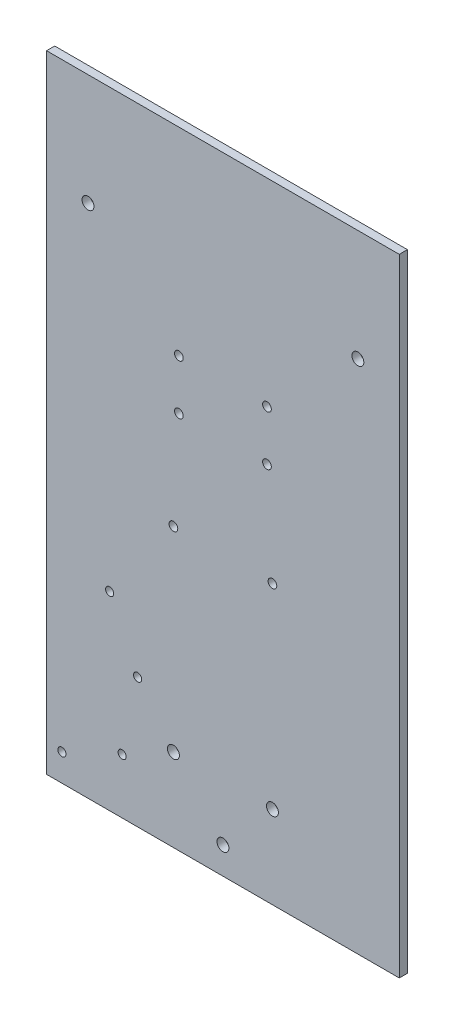
SolidWorks part; units mm, degrees
ref_plane "正面" through (0, 0, 0) normal (0, 0, 1) x (1, 0, 0)
ref_plane "平面" through (0, 0, 0) normal (0, 1, 0) x (1, 0, 0)
ref_plane "右側面" through (0, 0, 0) normal (1, 0, 0) x (0, 0, -1)
sketch "ｽｹｯﾁ1" plane through (0, 0, 0) normal (0, 0, 1) x (1, 0, 0)
  line L1 (-75, 115.5) -> (75, 115.5)
  line L2 (-75, 115.5) -> (-75, -115.5)
  line L3 (-75, -115.5) -> (75, -115.5)
  line L4 (75, 115.5) -> (75, -115.5)
  line L5 (-75, 115.5) -> (75, -115.5) construction
  line L6 (-75, -115.5) -> (75, 115.5) construction
  point P0 (0, 0)
  dimension "D1" = 231
  dimension "D2" = 150
extrude "ﾎﾞｽ - 押し出し1" add sketch "ｽｹｯﾁ1" along normal blind 12.5
sketch "ｽｹｯﾁ2" plane through (0, 0, 12.5) normal (0, 0, 1) x (1, 0, 0)
  line L0 (0, 115.5) -> (21.5, 115.5)
  line L1 (75, 115.5) -> (-75, 115.5) construction
  line L2 (0, 115.5) -> (-21.5, 115.5)
  line L3 (-21.5, 115.5) -> (-21.5, 13.5)
  line L4 (21.5, 115.5) -> (21.5, 13.5)
  line L5 (21.5, 13.5) -> (-21.5, 13.5)
  dimension "D1" = 21.5
  dimension "D2" = 21.5
  dimension "D3" = 102
extrude "ｶｯﾄ - 押し出し1" cut sketch "ｽｹｯﾁ2" against normal blind 10.5
sketch "ｽｹｯﾁ3" plane through (0, 0, 2) normal (0, 0, 1) x (1, 0, 0)
  line L0 (0, 115.5) -> (16.23, 115.5)
  line L1 (21.5, 115.5) -> (-21.5, 115.5) construction
  line L2 (0, 115.5) -> (-16.23, 115.5)
  line L3 (-16.23, 115.5) -> (-16.23, 42.5)
  line L4 (16.23, 115.5) -> (16.23, 42.5)
  line L5 (-16.23, 42.5) -> (-16.23, 24.1)
  line L6 (16.23, 42.5) -> (16.23, 24.1)
  line L7 (0, 115.5) -> (0, 110)
  circle A0 centre (-16.23, 42.5) radius 1.6
  circle A1 centre (16.23, 42.5) radius 1.6
  circle A2 centre (-16.23, 24.1) radius 1.6
  circle A3 centre (16.23, 24.1) radius 1.6
  circle A4 centre (0, 110) radius 4.4
  dimension "D5" = 3.2
  dimension "D6" = 3.2
  dimension "D9" = 3.2
  dimension "D10" = 3.2
  dimension "D12" = 8.8
  dimension "D1" = 16.23
  dimension "D2" = 16.23
  dimension "D3" = 73
  dimension "D4" = 73
  dimension "D7" = 18.4
  dimension "D8" = 18.4
  dimension "D11" = 5.5
sketch "ｽｹｯﾁ4" plane through (0, 0, 12.5) normal (0, 0, 1) x (1, 0, 0)
  line L0 (0, 115.5) -> (49.73, 115.5)
  line L1 (21.5, 115.5) -> (-21.5, 115.5) construction
  line L2 (75, 115.5) -> (21.5, 115.5) construction
  line L3 (0, 115.5) -> (-49.73, 115.5)
  line L4 (-21.5, 115.5) -> (-75, 115.5) construction
  line L5 (-49.73, 115.5) -> (-49.73, 74.5)
  line L6 (49.73, 115.5) -> (49.73, 74.5)
  circle A0 centre (-49.73, 74.5) radius 2.2
  circle A1 centre (49.73, 74.5) radius 2.2
  dimension "D5" = 4.4
  dimension "D6" = 4.4
  dimension "D1" = 49.73
  dimension "D2" = 49.73
  dimension "D3" = 41
  dimension "D4" = 41
extrude "ｶｯﾄ - 押し出し3" cut sketch "ｽｹｯﾁ4" against normal through all both and the other way through all
sketch "ｽｹｯﾁ5" plane through (0, 0, 12.5) normal (0, 0, 1) x (1, 0, 0)
  line L0 (0, 115.5) -> (18.25, 115.5)
  line L1 (21.5, 115.5) -> (-21.5, 115.5) construction
  line L2 (75, 115.5) -> (21.5, 115.5) construction
  line L3 (0, 115.5) -> (-18.25, 115.5)
  line L4 (-21.5, 115.5) -> (-75, 115.5) construction
  line L5 (-18.25, 115.5) -> (-18.25, -12.95)
  line L6 (18.25, 115.5) -> (18.25, -12.95)
  line L7 (-18.25, -12.95) -> (-18.25, -85)
  line L8 (18.25, -12.95) -> (18.25, -85)
  line L9 (0, -115.5) -> (0, -105.5)
  line L10 (-75, -115.5) -> (75, -115.5) construction
  line L11 (-18.25, -85) -> (-31.45, -85)
  line L12 (-31.45, -85) -> (-31.45, -67.68)
  line L13 (-31.45, -67.68) -> (-41.75, -67.68)
  line L14 (-41.75, -67.68) -> (-41.75, -45.48)
  line L15 (0, -105.5) -> (-37.14, -105.5)
  line L16 (-37.14, -105.5) -> (-37.14, -95.2)
  line L17 (-37.14, -105.5) -> (-59.34, -105.5)
  circle A0 centre (-18.25, -12.95) radius 1.6
  circle A1 centre (18.25, -12.95) radius 1.6
  circle A2 centre (-18.25, -85) radius 2.2
  circle A3 centre (18.25, -85) radius 2.2
  circle A4 centre (0, -105.5) radius 2.2
  circle A5 centre (-31.45, -67.68) radius 1.5
  circle A6 centre (-41.75, -45.48) radius 1.5
  circle A7 centre (-37.14, -95.2) radius 1.5
  circle A9 centre (-59.34, -105.5) radius 1.5
  dimension "D5" = 3.2
  dimension "D6" = 3.2
  dimension "D9" = 4.4
  dimension "D10" = 4.4
  dimension "D12" = 4.4
  dimension "D17" = 3
  dimension "D18" = 3
  dimension "D24" = 3
  dimension "D22" = 3
  dimension "D1" = 18.25
  dimension "D2" = 18.25
  dimension "D3" = 128.45
  dimension "D4" = 128.45
  dimension "D7" = 72.05
  dimension "D8" = 72.05
  dimension "D11" = 10
  dimension "D13" = 13.2
  dimension "D14" = 17.32
  dimension "D15" = 10.3
  dimension "D16" = 22.2
  dimension "D19" = 37.14
  dimension "D20" = 10.3
  dimension "D21" = 22.2
extrude "ｶｯﾄ - 押し出し4" cut sketch "ｽｹｯﾁ5" against normal through all
sketch "ｽｹｯﾁ6" plane through (0, 0, 2) normal (0, 0, 1) x (1, 0, 0)
  line L0 (0, 115.5) -> (0, 105.5)
  line L1 (0, 105.5) -> (12.5, 105.5)
  line L2 (0, 105.5) -> (-12.5, 105.5)
  circle A0 centre (-12.5, 105.5) radius 1.5
  circle A1 centre (12.5, 105.5) radius 1.5
  dimension "D4" = 3
  dimension "D5" = 3
  dimension "D1" = 12.5
  dimension "D2" = 12.5
  dimension "D3" = 10
extrude "ｶｯﾄ - 押し出し5" cut sketch "ｽｹｯﾁ6" against normal blind 10
extrude "ｶｯﾄ - 押し出し6" cut sketch "ｽｹｯﾁ3" against normal blind 10
sketch "ｽｹｯﾁ7" plane through (0, 0, 12.5) normal (0, 0, 1) x (1, 0, 0)
  line L0 (-21.5, 115.5) -> (-75, 115.5) construction
  line L1 (-75, -115.5) -> (-65, -115.5)
  line L2 (-75, -115.5) -> (-75, 115.5)
  line L3 (-75, 115.5) -> (-65, 115.5)
  line L4 (-65, -115.5) -> (-65, 115.5)
  line L5 (-75, -115.5) -> (75, -115.5) construction
  line L6 (75, -115.5) -> (48.25, -115.5)
  line L7 (75, -115.5) -> (75, 115.5)
  line L8 (75, 115.5) -> (48.25, 115.5)
  line L9 (48.25, -115.5) -> (48.25, 115.5)
  line L10 (75, -115.5) -> (75, 115.5) construction
  line L11 (75, 115.5) -> (21.5, 115.5) construction
  dimension "D1" = 10
extrude "ｶｯﾄ - 押し出し7" cut sketch "ｽｹｯﾁ7" against normal through all contours L2 L1 L4 L3
sketch "ｽｹｯﾁ8" plane through (0, 0, 12.5) normal (0, 0, 1) x (1, 0, 0)
  line L0 (75, 115.5) -> (21.5, 115.5) construction
  line L1 (75, -115.5) -> (65, -115.5)
  line L2 (75, -115.5) -> (75, 115.5)
  line L3 (75, 115.5) -> (65, 115.5)
  line L4 (65, -115.5) -> (65, 115.5)
  dimension "D1" = 10
extrude "ｶｯﾄ - 押し出し8" cut sketch "ｽｹｯﾁ8" against normal through all
sketch "ｽｹｯﾁ9" plane through (0, 0, 2) normal (0, 0, 1) x (1, 0, 0)
  line L1 (21.5, 13.5) -> (-21.5, 13.5)
  line L2 (21.5, 13.5) -> (21.5, 115.5)
  line L3 (21.5, 115.5) -> (-21.5, 115.5)
  line L4 (-21.5, 13.5) -> (-21.5, 115.5)
extrude "ﾎﾞｽ - 押し出し2" add sketch "ｽｹｯﾁ9" along normal blind 10.5
sketch "ｽｹｯﾁ10" plane through (0, 0, 0) normal (0, 0, -1) x (-1, 0, 0)
  circle A0 centre (-16.23, 24.1) radius 1.6
  circle A1 centre (-16.23, 42.5) radius 1.6
  circle A2 centre (16.23, 42.5) radius 1.6
  circle A3 centre (16.23, 24.1) radius 1.6
extrude "ｶｯﾄ - 押し出し9" cut sketch "ｽｹｯﾁ10" against normal blind 30 contours A1 | A0 | A2 | A3
sketch "ｽｹｯﾁ11" plane through (0, 0, 12.5) normal (0, 0, 1) x (1, 0, 0)
  line L0 (-65, -115.5) -> (65, -115.5) construction
  line L1 (65, -115.5) -> (-65, -115.5)
  line L2 (65, -115.5) -> (65, 115.5)
  line L3 (65, 115.5) -> (-65, 115.5)
  line L4 (-65, -115.5) -> (-65, 115.5)
extrude "ｶｯﾄ - 押し出し10" cut sketch "ｽｹｯﾁ11" against normal blind 9.5
